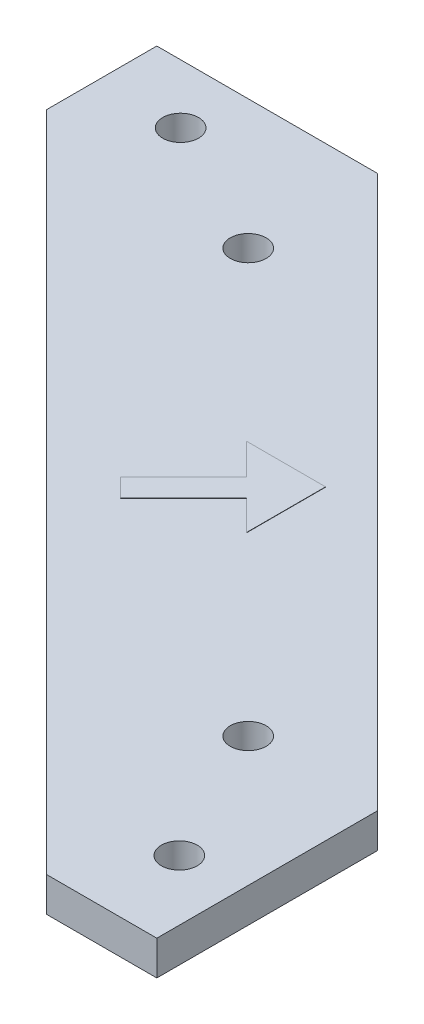
SolidWorks part; units mm, degrees
other "Markup2"
sketch "Sketch3" plane through (-71.12, 3.175, 71.12) normal (-0.1235, 0.7351, 0.6667) x (0.9905, 0.0505, 0.1278)
material "6061-T6 (SS)"
ref_plane "Front Plane" through (0, 0, 0) normal (0, 0, 1) x (1, 0, 0)
ref_plane "Top Plane" through (0, 0, 0) normal (0, 1, 0) x (1, 0, 0)
ref_plane "Right Plane" through (0, 0, 0) normal (1, 0, 0) x (0, 0, -1)
sketch "Sketch1" plane through (0, 0, 0) normal (0, 1, 0) x (1, 0, 0)
  line L0 (0, 0) -> (-50.8, 0) construction
  line L5 (-50.8, 0) -> (-63.5, 0) construction
  line L6 (-25.4, 0) -> (-25.4, -17.4625) construction
  line L8 (0, 0) -> (0, -50.8) construction
  line L9 (0, -50.8) -> (0, -63.5) construction
  line L10 (0, 0) -> (0, -25.4) construction
  line L11 (0, -25.4) -> (-17.4625, -25.4) construction
  line L12 (-50.8, 0) -> (0, -50.8)
  line L13 (0, 0) -> (-71.12, 0)
  line L14 (0, 0) -> (0, -71.12)
  line L17 (-71.12, 0) -> (-71.12, -10.16)
  line L18 (-71.12, -10.16) -> (-10.16, -71.12)
  line L19 (0, -71.12) -> (-10.16, -71.12)
  line L20 (-8.7312, -25.4) -> (-8.7312, -50.8) construction
  line L21 (-8.7312, -50.8) -> (-11.9062, -50.8) construction
  line L22 (-5.5562, -63.4921) -> (-5.5562, -76.1921) construction
  line L23 (-8.7312, -50.8) -> (-5.5562, -50.8) construction
  line L24 (-5.5562, -50.8) -> (-5.5562, -63.4921) construction
  line L25 (-25.4, -8.7313) -> (-50.8, -8.7313) construction
  line L28 (-50.8, -8.7313) -> (-50.8, -11.9062) construction
  circle A6 centre (-11.9062, -50.8) radius 1.651
  circle A7 centre (-5.5562, -63.4921) radius 1.651
  circle A8 centre (-50.8, -11.9062) radius 1.651
  circle A9 centre (-63.5, -5.4293) radius 1.651
  point P1 (-50.0155, 0)
  point P7 (0, -50.0548)
  point P9 (-8.7312, -25.4)
  point P24 (-8.7312, -50.8)
  point P38 (-50.8, -8.7313)
  point P41 (-25.4, 0)
  dimension "D4" = 3.302
  dimension "D10" = 25.4
  dimension "D11" = 3.302
  dimension "D12" = 3.302
  dimension "D25" = 3.302
  dimension "D26" = 3.302
  dimension "D1" = 50.8
  dimension "D5" = 17.4625
  dimension "D6" = 12.7
  dimension "D7" = 50.8
  dimension "D8" = 12.7
  dimension "D9" = 25.4
  dimension "D13" = 25.4
  dimension "D15" = 10.16
  dimension "D16" = 10.16
  dimension "D18" = 7.62
  dimension "D19" = 12.7
  dimension "D20" = 12.6921
  dimension "D21" = 3.175
  dimension "D22" = 3.175
  dimension "D28" = 3.175
  dimension "D30" = 25.4
extrude "Boss-Extrude2" add sketch "Sketch1" along normal blind 3.175
sketch "Sketch5" plane through (0, 3.175, 0) normal (0, 1, 0) x (1, 0, 0)
  line L0 (-25.4, -25.4) -> (-28.186, -27.4009) construction
  line L1 (-28.186, -27.4009) -> (-35.4749, -27.4009)
  line L2 (-28.186, -27.4009) -> (-28.186, -34.6898)
  line L5 (-50.8, 0) -> (0, -50.8) construction
  line L6 (-35.4749, -27.4009) -> (-32.5954, -30.2803)
  line L7 (-28.186, -34.6898) -> (-30.9407, -31.9351)
  line L9 (-32.5954, -30.2803) -> (-38.3847, -36.0696)
  line L10 (-30.9407, -31.9351) -> (-36.73, -37.7243)
  line L11 (-38.3847, -36.0696) -> (-36.73, -37.7243)
  point P1 (-25.4, -24.239)
  point P5 (-25.4, -24.239)
  point P12 (0, 0)
  point P13 (-24.8994, -24.239)
  point P14 (-25.7581, -25.4)
  point P15 (-28.186, -27.4009)
extrude "Boss-Extrude3" add sketch "Sketch5" along normal blind 0.0254
equation "\"D15\"=0.65"
